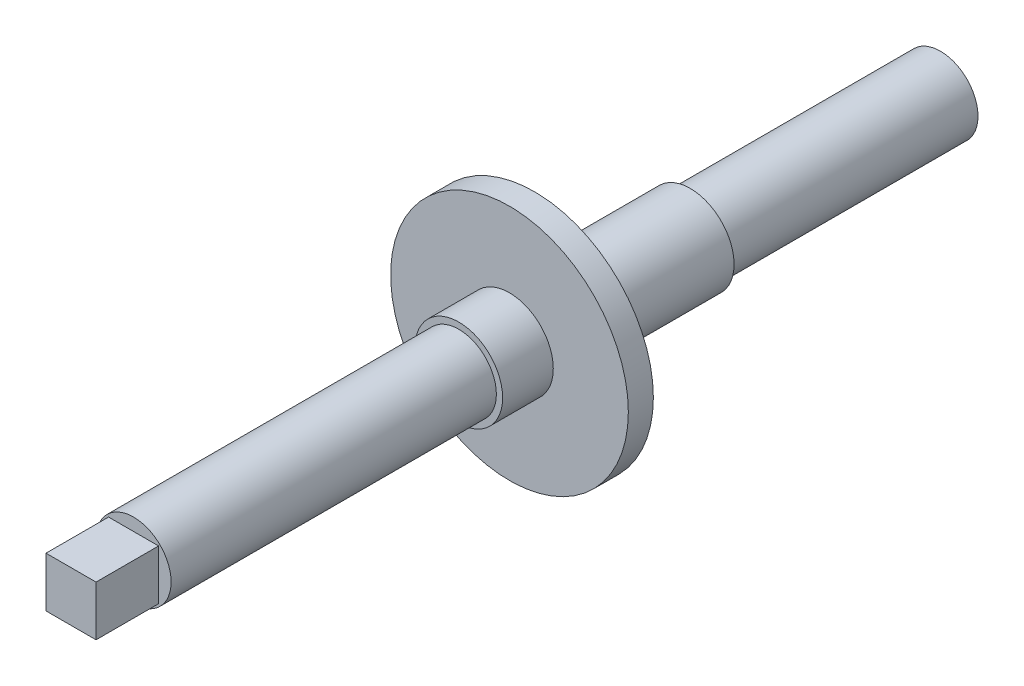
SolidWorks part; units mm, degrees
material "1.5810 (18NiCr5-4)"
ref_plane "Alzado" through (0, 0, 0) normal (0, 0, 1) x (1, 0, 0)
ref_plane "Planta" through (0, 0, 0) normal (0, 1, 0) x (1, 0, 0)
ref_plane "Vista lateral" through (0, 0, 0) normal (1, 0, 0) x (0, 0, -1)
sketch "Croquis1" plane through (0, 0, 0) normal (0, 0, 1) x (1, 0, 0)
  circle A0 centre (0, 0) radius 3
extrude "Saliente-Extruir1" add sketch "Croquis1" along normal blind 20
sketch "Croquis2" plane through (0, 0, 20) normal (0, 0, 1) x (1, 0, 0)
  circle A0 centre (0, 0) radius 3.5
extrude "Saliente-Extruir2" add sketch "Croquis2" along normal blind 12.45
sketch "Croquis3" plane through (0, 0, 32.45) normal (0, 0, 1) x (1, 0, 0)
  circle A0 centre (0, 0) radius 9.5
extrude "Saliente-Extruir3" add sketch "Croquis3" along normal blind 2
sketch "Croquis4" plane through (0, 0, 34.45) normal (0, 0, 1) x (1, 0, 0)
  circle A0 centre (0, 0) radius 3.5
extrude "Saliente-Extruir4" add sketch "Croquis4" along normal blind 4.05
sketch "Croquis5" plane through (0, 0, 38.5) normal (0, 0, 1) x (1, 0, 0)
  circle A0 centre (0, 0) radius 3
extrude "Saliente-Extruir5" add sketch "Croquis5" along normal blind 26
sketch "Croquis6" plane through (0, 0, 64.5) normal (0, 0, 1) x (1, 0, 0)
  line L1 (-2, -2) -> (2, -2)
  line L2 (-2, -2) -> (-2, 2)
  line L3 (-2, 2) -> (2, 2)
  line L4 (2, -2) -> (2, 2)
  line L5 (-2, -2) -> (2, 2) construction
  line L6 (-2, 2) -> (2, -2) construction
  point P0 (0, 0)
  dimension "D1" = 4
  dimension "D2" = 4
extrude "Saliente-Extruir6" add sketch "Croquis6" along normal blind 5
